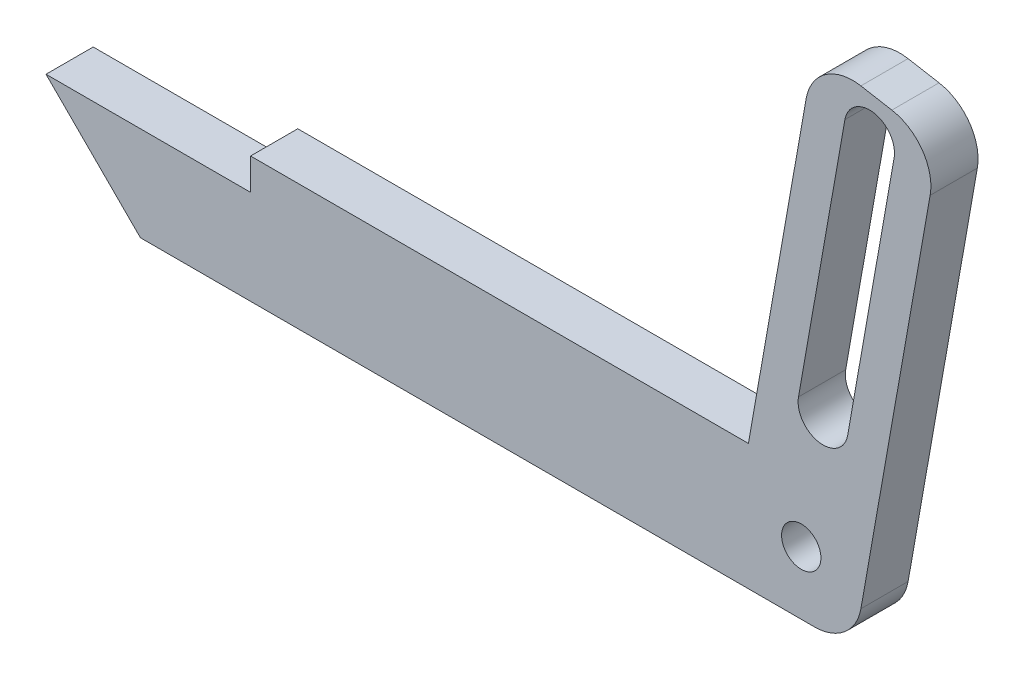
SolidWorks part; units mm, degrees
material "1060 Alloy"
ref_plane "Front Plane" through (0, 0, 0) normal (0, 0, 1) x (1, 0, 0)
ref_plane "Top Plane" through (0, 0, 0) normal (0, 1, 0) x (1, 0, 0)
ref_plane "Right Plane" through (0, 0, 0) normal (1, 0, 0) x (0, 0, -1)
sketch "Sketch1" plane through (0, 0, 0) normal (0, 0, 1) x (1, 0, 0)
  line L0 (-56.0248, -23.4823) -> (-9.3848, -23.4823)
  line L1 (-9.3848, -23.4823) -> (-5.1929, 0.2909)
  line L2 (-5.1929, 0.2909) -> (2.6856, -1.0982)
  line L3 (2.6856, -1.0982) -> (-2.672, -31.4823)
  line L4 (-56.0248, -23.4823) -> (-48.0248, -31.4823)
  line L5 (-2.672, -31.4823) -> (-48.0248, -31.4823)
extrude "Boss-Extrude1" add sketch "Sketch1" along normal blind 3
sketch "Sketch2" plane through (0, 0, 3) normal (0, 0, 1) x (1, 0, 0)
  line L0 (-56.0248, -23.4823) -> (-41.0248, -23.4823)
  line L1 (-9.3848, -23.4823) -> (-56.0248, -23.4823) construction
  line L2 (-41.0248, -23.4823) -> (-41.0248, -25.4823)
  line L3 (-41.0248, -25.4823) -> (-54.0248, -25.4823)
  line L4 (-56.0248, -23.4823) -> (-48.0248, -31.4823) construction
  line L5 (-54.0248, -25.4823) -> (-56.0248, -23.4823)
  line L6 (2.6856, -1.0982) -> (-5.1929, 0.2909) construction
  line L7 (-3.2512, -2.59) -> (-6.2032, -19.3317)
  line L8 (-0.1244, -3.1413) -> (-3.0764, -19.8831)
  arc A0 (-0.1244, -3.1413) -> (-3.2512, -2.59) centre (-1.6878, -2.8657) ccw
  arc A1 (-6.2032, -19.3317) -> (-3.0764, -19.8831) centre (-4.6398, -19.6074) ccw
  circle A2 centre (-6.0284, -27.4823) radius 1.25
  dimension "D1" = 2.5
extrude "Cut-Extrude1" cut sketch "Sketch2" against normal blind 3
fillet "Fillet1" radius 3 3 edges at (-2.672, -31.4823, 1.5) (-5.1929, 0.2909, 1.5) (2.6856, -1.0982, 1.5)
